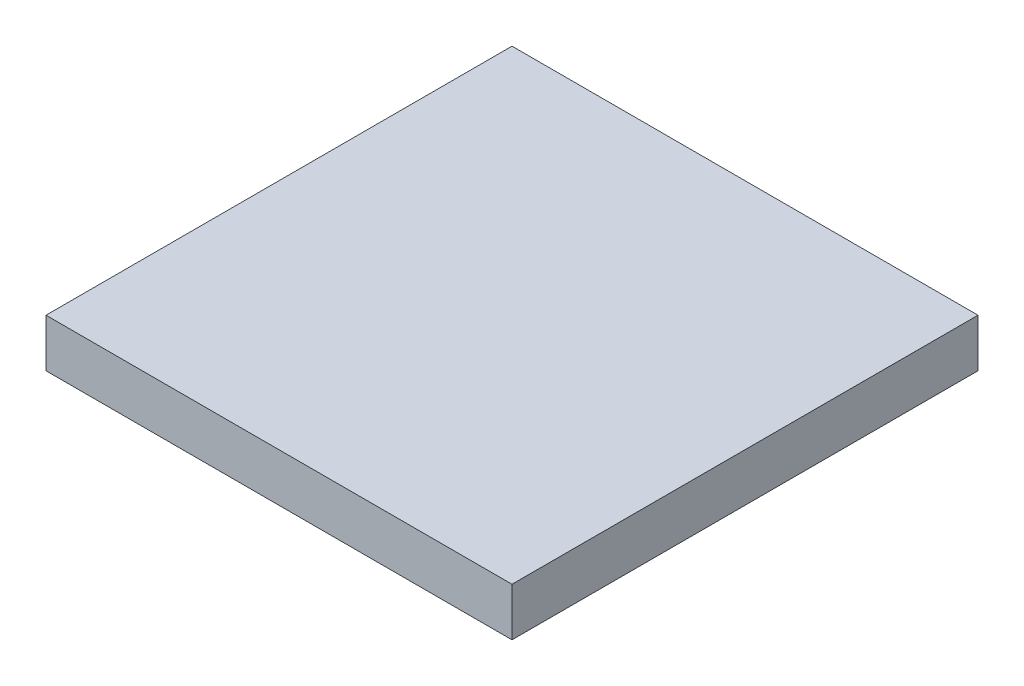
SolidWorks part; units mm, degrees
ref_plane "Front Plane" through (0, 0, 0) normal (0, 0, 1) x (1, 0, 0)
ref_plane "Top Plane" through (0, 0, 0) normal (0, 1, 0) x (1, 0, 0)
ref_plane "Right Plane" through (0, 0, 0) normal (1, 0, 0) x (0, 0, -1)
sketch "Sketch2" plane through (0, 0, 0) normal (0, 1, 0) x (1, 0, 0)
  line L1 (-114.3, -114.3) -> (114.3, -114.3)
  line L2 (-114.3, -114.3) -> (-114.3, 114.3)
  line L3 (-114.3, 114.3) -> (114.3, 114.3)
  line L4 (114.3, -114.3) -> (114.3, 114.3)
  line L5 (-114.3, -114.3) -> (114.3, 114.3) construction
  line L6 (-114.3, 114.3) -> (114.3, -114.3) construction
  point P0 (0, 0)
  dimension "D1" = 228.6
  dimension "D2" = 228.6
extrude "Boss-Extrude1" add sketch "Sketch2" along normal blind 23.622
